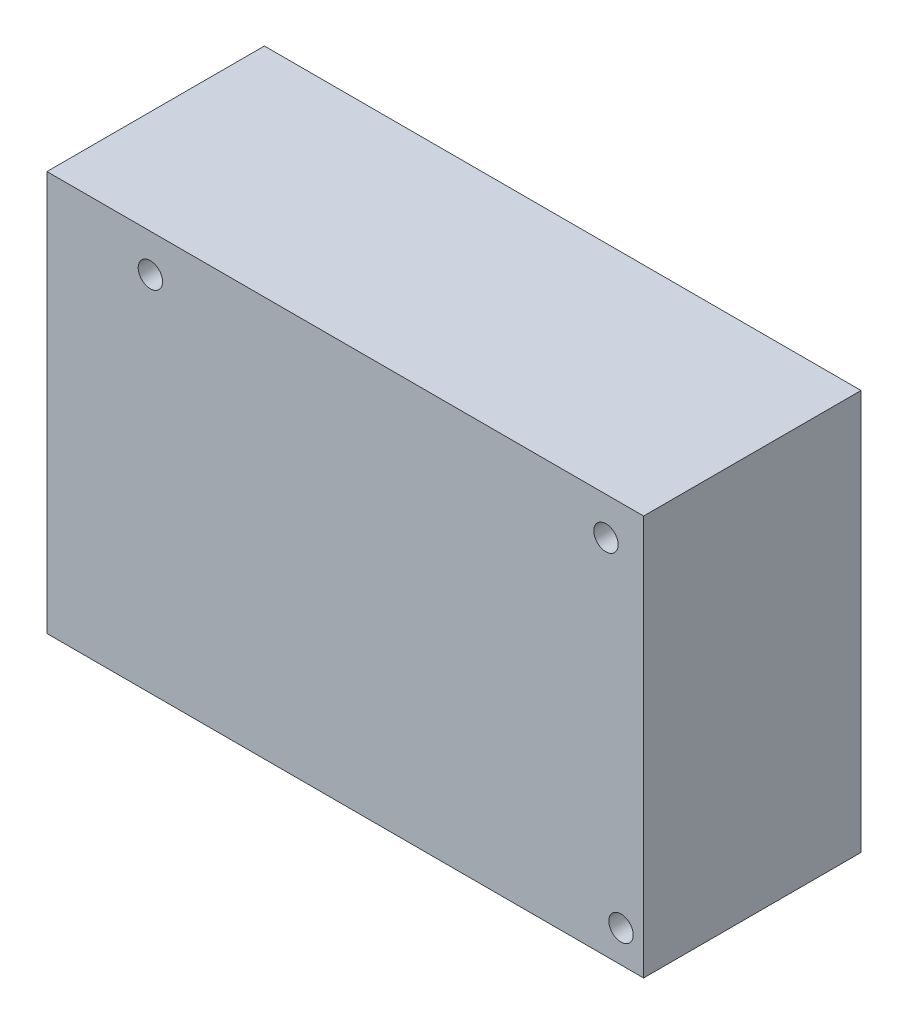
SolidWorks part; units mm, degrees
ref_plane "Front Plane" through (0, 0, 0) normal (0, 0, 1) x (1, 0, 0)
ref_plane "Top Plane" through (0, 0, 0) normal (0, 1, 0) x (1, 0, 0)
ref_plane "Right Plane" through (0, 0, 0) normal (1, 0, 0) x (0, 0, -1)
sketch "Sketch1" plane through (0, 0, 0) normal (0, 0, 1) x (1, 0, 0)
  line L1 (43.561, -29.21) -> (-43.561, -29.21)
  line L2 (43.561, -29.21) -> (43.561, 29.21)
  line L3 (43.561, 29.21) -> (-43.561, 29.21)
  line L4 (-43.561, -29.21) -> (-43.561, 29.21)
  line L5 (43.561, -29.21) -> (-43.561, 29.21) construction
  line L6 (43.561, 29.21) -> (-43.561, -29.21) construction
  point P0 (0, 0)
  dimension "D1" = 87.122
  dimension "D2" = 58.42
extrude "Boss-Extrude1" add sketch "Sketch1" along normal blind 31.75
sketch "Sketch2" plane through (0, 0, 31.75) normal (0, 0, 1) x (1, 0, 0)
  line L0 (43.561, -29.21) -> (43.561, 29.21) construction
  line L1 (43.561, 29.21) -> (-43.561, 29.21) construction
  line L2 (-43.561, -29.21) -> (43.561, -29.21) construction
  circle A0 centre (-28.4607, 23.7109) radius 1.778
  circle A1 centre (38.0619, 23.7109) radius 1.778
  circle A2 centre (40.259, -24.5364) radius 1.778
  dimension "D1" = 3.556
  dimension "D5" = 3.556
  dimension "D2" = 66.5226
  dimension "D3" = 5.4991
  dimension "D4" = 5.4991
  dimension "D6" = 4.6736
  dimension "D7" = 3.302
extrude "Cut-Extrude1" cut sketch "Sketch2" against normal through all
